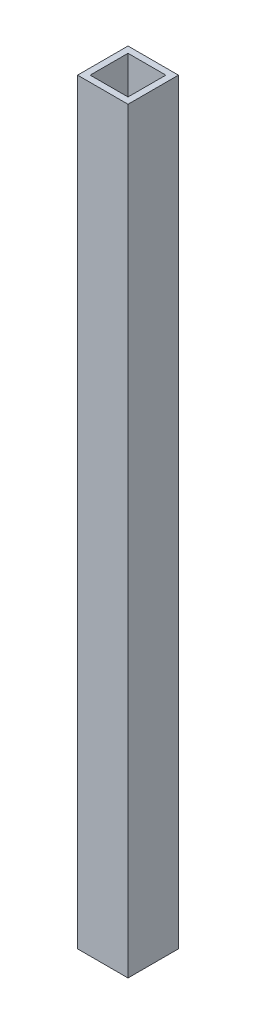
SolidWorks part; units mm, degrees
material "1060 Alloy"
ref_plane "Front Plane" through (0, 0, 0) normal (0, 0, 1) x (1, 0, 0)
ref_plane "Top Plane" through (0, 0, 0) normal (0, 1, 0) x (1, 0, 0)
ref_plane "Right Plane" through (0, 0, 0) normal (1, 0, 0) x (0, 0, -1)
sketch "Sketch1" plane through (0, 0, 0) normal (0, 1, 0) x (1, 0, 0)
  line L1 (-12.7, 12.7) -> (12.7, 12.7)
  line L2 (-12.7, 12.7) -> (-12.7, -12.7)
  line L3 (-12.7, -12.7) -> (12.7, -12.7)
  line L4 (12.7, 12.7) -> (12.7, -12.7)
  line L5 (-12.7, 12.7) -> (12.7, -12.7) construction
  line L6 (-12.7, -12.7) -> (12.7, 12.7) construction
  point P0 (0, 0)
  dimension "D1" = 25.4
  dimension "D2" = 25.4
extrude "Boss-Extrude1" add sketch "Sketch1" along normal blind 381
sketch "Sketch2" plane through (0, 381, 0) normal (0, 1, 0) x (1, 0, 0)
  line L1 (-9.525, 9.525) -> (9.525, 9.525)
  line L2 (-9.525, 9.525) -> (-9.525, -9.525)
  line L3 (-9.525, -9.525) -> (9.525, -9.525)
  line L4 (9.525, 9.525) -> (9.525, -9.525)
  line L5 (-9.525, 9.525) -> (9.525, -9.525) construction
  line L6 (-9.525, -9.525) -> (9.525, 9.525) construction
  point P0 (0, 0)
  dimension "D1" = 19.05
  dimension "D2" = 19.05
extrude "Cut-Extrude1" cut sketch "Sketch2" against normal through all both and the other way through all
